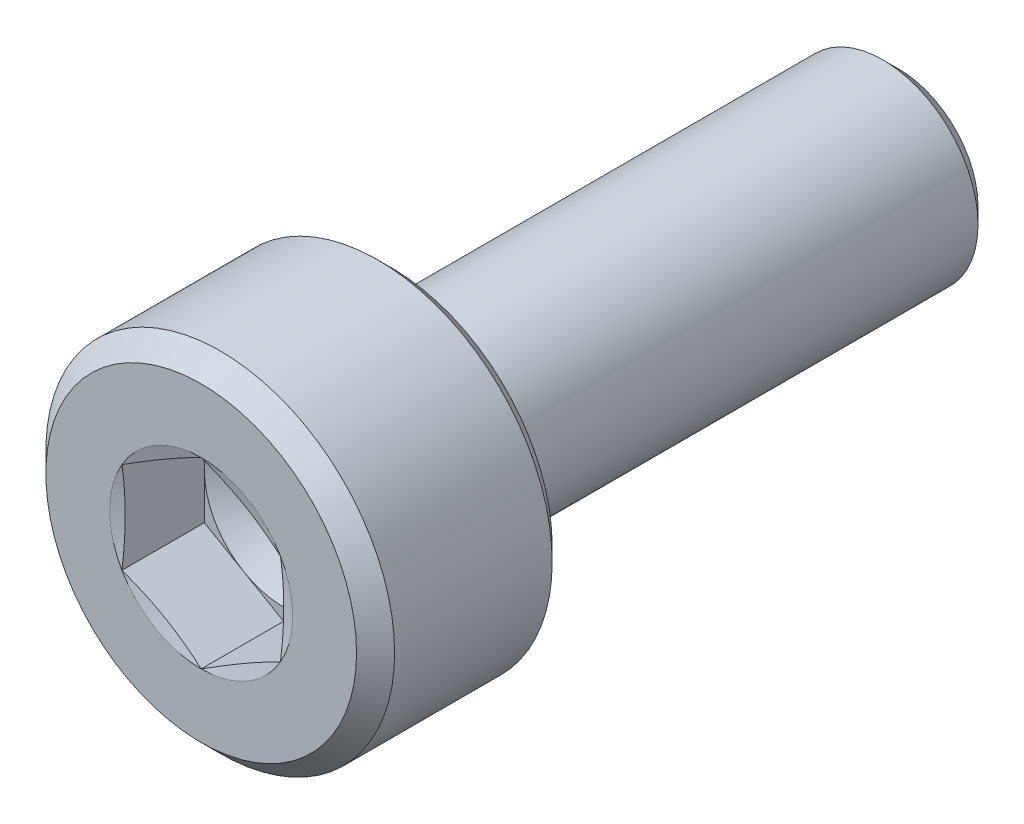
SolidWorks part; units mm, degrees
ref_plane "Front Plane" through (0, 0, 0) normal (0, 0, 1) x (1, 0, 0)
ref_plane "Top Plane" through (0, 0, 0) normal (0, 1, 0) x (1, 0, 0)
ref_plane "Right Plane" through (0, 0, 0) normal (1, 0, 0) x (0, 0, -1)
sketch "Sketch1" plane through (0, 0, 0) normal (1, 0, 0) x (0, 0, -1)
  line L0 (0, 0) -> (12.9407, 0) construction
  line L1 (0, 0) -> (0, 2.45)
  line L2 (0, 2.45) -> (0.3, 2.75)
  line L3 (0.3, 2.75) -> (2.785, 2.75)
  line L4 (3, 2.535) -> (3, 1.8)
  line L5 (3.51, 1.5) -> (10.75, 1.5)
  line L6 (10.75, 1.5) -> (11, 1.25)
  line L7 (11, 1.25) -> (11, 0)
  line L8 (11, 0) -> (0, 0)
  line L9 (2.785, 2.75) -> (3, 2.535)
  line L10 (3.4662, 1.5101) -> (3.0562, 1.7101)
  arc A2 (3.51, 1.5) -> (3.4662, 1.5101) centre (3.51, 1.6) cw
  arc A3 (3.0562, 1.7101) -> (3, 1.8) centre (3.1, 1.8) cw
  point P6 (3, 2.75)
  dimension "R2" = 0.1
  dimension "R1" = 0.1
  dimension "D1" = 45
  dimension "DK" = 5.5
  dimension "D3" = 45
  dimension "length" = 8
  dimension "K" = 3
  dimension "V" = 0.3
  dimension "HOLESIZE" = 3
  dimension "D4" = 2.5
  dimension "D5" = 45
  dimension "DW" = 5.07
  dimension "F" = 0.51
  dimension "DA" = 3.6
revolve "Revolve1" add sketch "Sketch1" angle 360 about L0
cosmetic thread "Cosmetic Thread1" parameters "D1"=6.5, "D2"=3
sketch "Sketch2" plane through (0, 0, 0) normal (0, 0, 1) x (1, 0, 0)
  line L0 (0, 0) -> (0, 1.4434) construction
  line L2 (0, 1.4434) -> (-1.25, 0.7217)
  line L3 (-1.25, 0.7217) -> (-1.25, -0.7217)
  line L4 (-1.25, -0.7217) -> (0, -1.4434)
  line L5 (0, -1.4434) -> (1.25, -0.7217)
  line L6 (1.25, -0.7217) -> (1.25, 0.7217)
  line L7 (1.25, 0.7217) -> (0, 1.4434)
  circle A0 centre (0, 0) radius 1.25 construction
  dimension "S" = 2.5
extrude "Cut-Extrude1" cut sketch "Sketch2" against normal blind 1.3
sketch "Sketch3" plane through (0, 0, 0) normal (1, 0, 0) x (0, 0, -1)
  line L0 (1.3, 0) -> (11, 0) construction
  line L1 (11, -1.25) -> (11, 1.25) construction
  line L2 (1.3, 0) -> (1.3, 1.25)
  line L4 (1.3, 1.25) -> (2.0217, 0)
  line L5 (2.0217, 0) -> (1.3, 0)
  line L6 (0, 2.45) -> (0, -2.45) construction
  dimension "DRILLANG" = 60
  dimension "DRILL DEPTH" = 1.3
  dimension "S2" = 2.5
revolve "Cut-Revolve2" cut sketch "Sketch3" angle 360 about L0
sketch "Sketch4" plane through (0, 0, 0) normal (1, 0, 0) x (0, 0, -1)
  line L0 (0, 0) -> (4.6121, 0) construction
  line L1 (0, 1.4434) -> (0, 1.25)
  line L2 (0, 2.45) -> (0, -2.45) construction
  line L3 (0, 1.25) -> (0.0518, 1.25)
  line L4 (0.0518, 1.25) -> (0, 1.4434)
  point P12 (0.0259, 1.25)
  dimension "D1" = 2.5
  dimension "D2" = 15
revolve "Cut-Revolve3" cut sketch "Sketch4" angle 360 about L0
